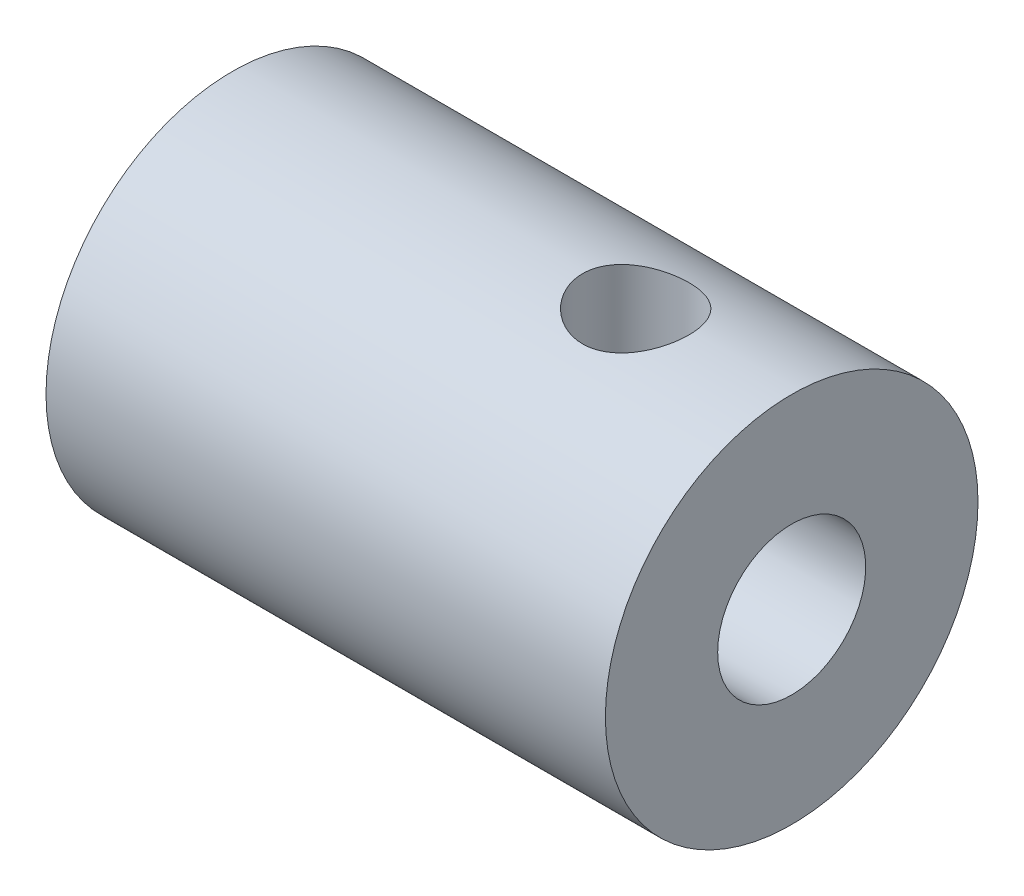
SolidWorks part; units mm, degrees
ref_plane "Front" through (0, 0, 0) normal (0, 0, 1) x (1, 0, 0)
ref_plane "Top" through (0, 0, 0) normal (0, 1, 0) x (1, 0, 0)
ref_plane "Right" through (0, 0, 0) normal (1, 0, 0) x (0, 0, -1)
sketch "Sketch3" plane through (0, 0, 0) normal (0, 0, 1) x (1, 0, 0)
  line L0 (-6.35, 4.7625) -> (-6.35, 3.175)
  line L1 (-6.35, 3.175) -> (0, 3.175)
  line L2 (0, 3.175) -> (0, 1.8923)
  line L3 (0, 1.8923) -> (7.9502, 1.8923)
  line L4 (7.9502, 1.8923) -> (7.9502, 4.7625)
  line L5 (7.9502, 4.7625) -> (-6.35, 4.7625)
  line L6 (0, 0) -> (7.9502, 0) construction
  point P7 (0, 0)
  dimension "D1" = 4.7625
  dimension "D2" = 1.8923
  dimension "D3" = 3.175
  dimension "D4" = 14.3002
  dimension "D5" = 6.35
revolve "Revolve1" add sketch "Sketch3" angle 360 about L6
sketch "Sketch4" plane through (0, 0, 0) normal (0, 1, 0) x (1, 0, 0)
  line L0 (-6.35, 4.7625) -> (-6.35, -4.7625) construction
  circle A0 centre (3.9624, 0) radius 1.3589
  dimension "D1" = 10.3124
  dimension "D2" = 2.7178
extrude "Cut-Extrude1" cut sketch "Sketch4" against normal through all both and the other way through all
